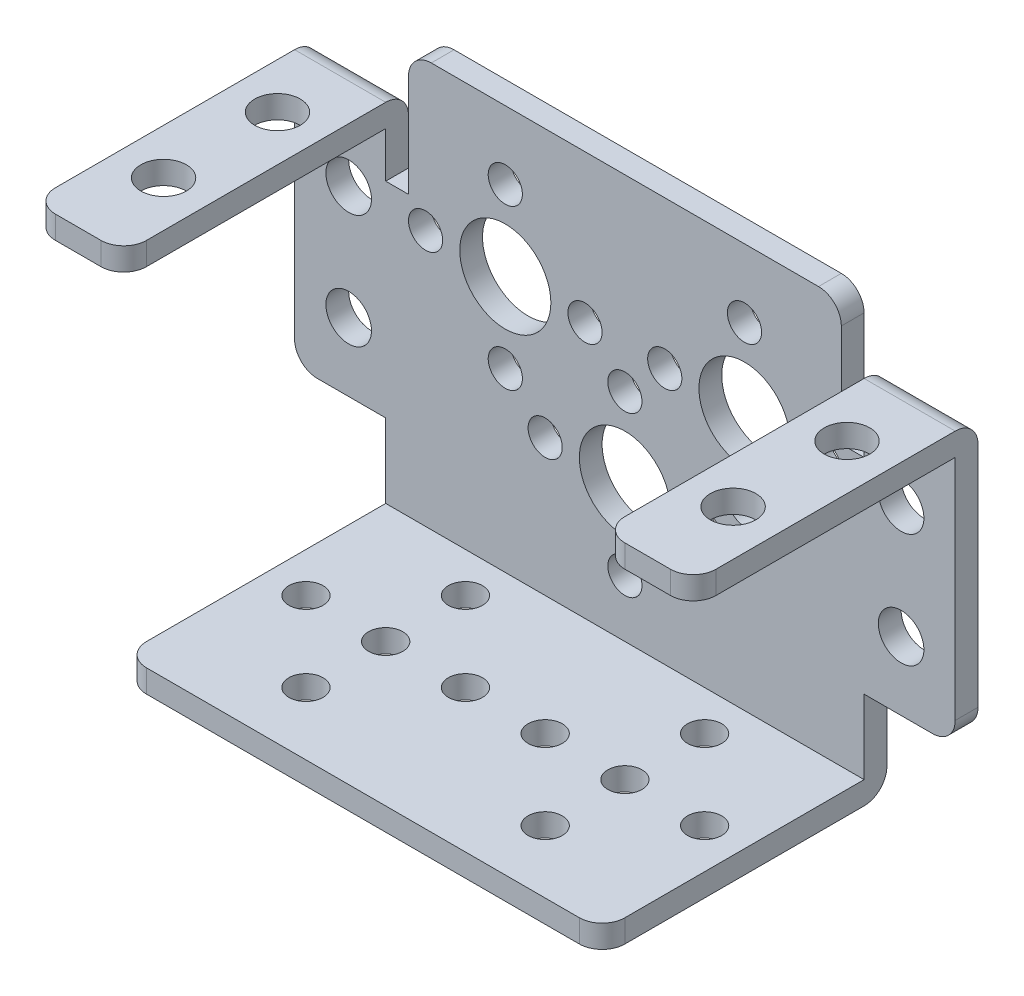
SolidWorks part; units mm, degrees
material "Hierro dúctil (SN)"
ref_plane "Alzado" through (0, 0, 0) normal (0, 0, 1) x (1, 0, 0)
ref_plane "Planta" through (0, 0, 0) normal (0, 1, 0) x (1, 0, 0)
ref_plane "Vista lateral" through (0, 0, 0) normal (1, 0, 0) x (0, 0, -1)
sketch "Croquis1" plane through (0, 0, 0) normal (0, 0, 1) x (1, 0, 0)
  line L1 (-21, -12) -> (21, -12)
  line L2 (21, -12) -> (21, -5.5)
  line L3 (29, -3.5) -> (29, 16.5)
  line L4 (29, 16.5) -> (21, 16.5)
  line L5 (21, 16.5) -> (21, 12.5)
  line L6 (21, 12.5) -> (19, 12.5)
  line L7 (19, 12.5) -> (19, 21.49)
  line L8 (17, 23.49) -> (-17, 23.49)
  line L9 (-19, 21.49) -> (-19, 12.5)
  line L10 (-19, 12.5) -> (-21, 12.5)
  line L11 (-21, 12.5) -> (-21, 16.5)
  line L12 (-21, 16.5) -> (-29, 16.5)
  line L13 (-29, 16.5) -> (-29, -3.5)
  line L14 (21, -5.5) -> (27, -5.5)
  line L16 (-27, -5.5) -> (-21, -5.5)
  line L17 (-21, -5.5) -> (-21, -12)
  circle A0 centre (0, 7) radius 1.5
  circle A1 centre (7, 0) radius 1.5
  circle A2 centre (0, -7) radius 1.5
  circle A3 centre (-7, 0) radius 1.5
  circle A4 centre (-24.25, 10.5) radius 2
  circle A5 centre (24.25, 10.5) radius 2
  circle A6 centre (0, 0) radius 7 construction
  circle A7 centre (-24.25, 0.5) radius 2
  circle A8 centre (0, 0) radius 4
  circle A9 centre (10.5, 10.5) radius 7 construction
  circle A10 centre (10.5, 17.5) radius 1.5
  circle A11 centre (17.5, 10.5) radius 1.5
  circle A12 centre (10.5, 3.5) radius 1.5
  circle A13 centre (3.5, 10.5) radius 1.5
  circle A14 centre (-10.5, 17.5) radius 1.5
  circle A15 centre (-3.5, 10.5) radius 1.5
  circle A16 centre (-10.5, 3.5) radius 1.5
  circle A17 centre (-17.5, 10.5) radius 1.5
  circle A18 centre (-10.5, 10.5) radius 7 construction
  circle A19 centre (-10.5, 10.5) radius 4
  circle A20 centre (10.5, 10.5) radius 4
  circle A21 centre (24.25, 0.5) radius 2
  arc A22 (19, 21.49) -> (17, 23.49) centre (17, 21.49) ccw
  arc A23 (-17, 23.49) -> (-19, 21.49) centre (-17, 21.49) ccw
  arc A24 (29, -3.5) -> (27, -5.5) centre (27, -3.5) cw
  arc A25 (-29, -3.5) -> (-27, -5.5) centre (-27, -3.5) ccw
  point P13 (0, 23.49)
  point P15 (0, -12)
  point P17 (0, 0)
  point P34 (0, -5.5)
  point P64 (19, 23.49)
  point P67 (-19, 23.49)
  dimension "D1" = 14
  dimension "D2" = 3
  dimension "D4" = 8
  dimension "D7" = 4
  dimension "D19" = 2
  dimension "D5" = 10
  dimension "D6" = 10.5
  dimension "D3" = 38
  dimension "D8" = 35.49
  dimension "D9" = 12
  dimension "D10" = 12.5
  dimension "D11" = 21
  dimension "D12" = 28.5
  dimension "D13" = 29
  dimension "D14" = 29
  dimension "D15" = 24.25
  dimension "D16" = 48.5
  dimension "D17" = 8
  dimension "D18" = 4
extrude "Saliente-Extruir1" add sketch "Croquis1" along normal blind 2
sketch "Croquis2" plane through (0, 0, 0) normal (0, 0, 1) x (1, 0, 0)
  line L0 (-21, -12) -> (21, -12)
  line L1 (21, -12) -> (21, -14)
  line L2 (21, -14) -> (-21, -14)
  line L3 (-21, -14) -> (-21, -12)
  line L4 (-29, 16.5) -> (-29, 18.5)
  line L5 (-29, 18.5) -> (-21, 18.5)
  line L6 (-21, 18.5) -> (-21, 16.5)
  line L7 (-21, 16.5) -> (-29, 16.5)
  line L8 (21, 16.5) -> (21, 18.5)
  line L9 (21, 18.5) -> (29, 18.5)
  line L10 (29, 18.5) -> (29, 16.5)
  line L11 (29, 16.5) -> (21, 16.5)
  dimension "D1" = 2
extrude "Saliente-Extruir2" add sketch "Croquis2" along normal blind 25
fillet "Redondeo2" radius 2 9 edges at (-21, -13, 25) (21, -13, 25) (29, 17.5, 25) (21, 17.5, 25) (-21, 17.5, 25) (-29, 17.5, 25) (-25, 18.5, 0) (0, -14, 0) (25, 18.5, 0)
sketch "Croquis3" plane through (0, 0, 0) normal (0, 1, 0) x (1, 0, 0)
  line L0 (0, -12.5) -> (0, 0) construction
  line L1 (21, -23) -> (21, -2) construction
  line L2 (-21, -12.5) -> (-29, -12.5) construction
  line L3 (0, -12.5) -> (-21, -12.5) construction
  line L4 (-21, -23) -> (-21, -2) construction
  line L5 (0, -12.5) -> (21, -12.5) construction
  line L6 (-29, -23) -> (-29, -2) construction
  line L7 (0, -12.5) -> (0, -25) construction
  line L8 (19, -25) -> (-19, -25) construction
  line L9 (21, -12.5) -> (29, -12.5) construction
  line L10 (29, -23) -> (29, -2) construction
  circle A0 centre (-10.5, -12.5) radius 1.5
  circle A1 centre (10.5, -12.5) radius 1.5
  circle A2 centre (-10.5, -12.5) radius 7 construction
  circle A3 centre (10.5, -12.5) radius 7 construction
  circle A4 centre (-10.5, -5.5) radius 1.5
  circle A5 centre (-3.5, -12.5) radius 1.5
  circle A6 centre (-10.5, -19.5) radius 1.5
  circle A7 centre (-17.5, -12.5) radius 1.5
  circle A8 centre (3.5, -12.5) radius 1.5
  circle A9 centre (10.5, -19.5) radius 1.5
  circle A10 centre (10.5, -5.5) radius 1.5
  circle A11 centre (17.5, -12.5) radius 1.5
  circle A12 centre (-25, -7.5) radius 2
  circle A13 centre (-25, -17.5) radius 2
  circle A14 centre (25, -17.5) radius 2
  circle A15 centre (25, -7.5) radius 2
  point P42 (25, -12.5)
  point P49 (-25, -12.5)
  dimension "D1" = 3
  dimension "D2" = 14
  dimension "D3" = 4
  dimension "D4" = 5
  dimension "D5" = 10
extrude "Cortar-Extruir1" cut sketch "Croquis3" against normal blind 25 and the other way blind 25
